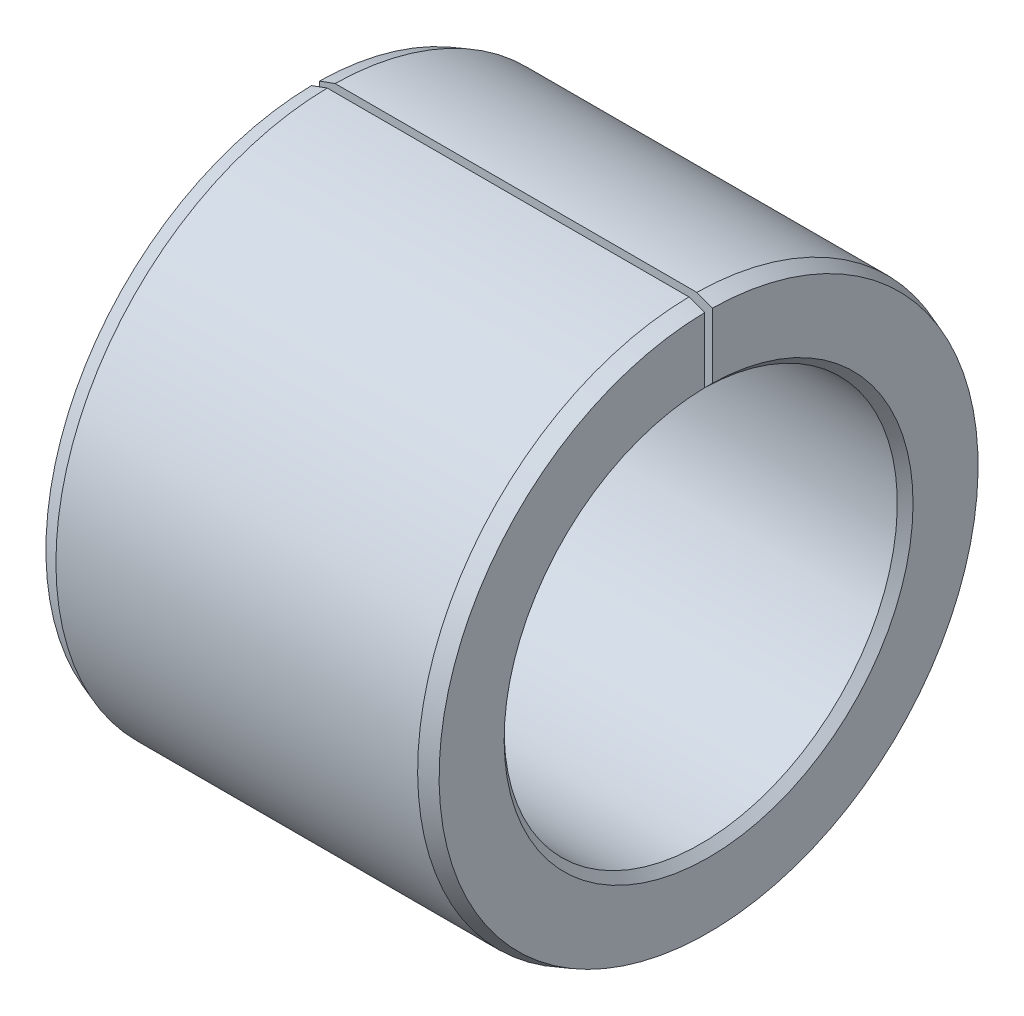
SolidWorks part; units mm, degrees
ref_plane "前视基准面" through (0, 0, 0) normal (0, 0, 1) x (1, 0, 0)
ref_plane "上视基准面" through (0, 0, 0) normal (0, 1, 0) x (1, 0, 0)
ref_plane "右视基准面" through (0, 0, 0) normal (1, 0, 0) x (0, 0, -1)
sketch "草图1" plane through (0, 0, 0) normal (0, 0, 1) x (1, 0, 0)
  line L0 (0, 0) -> (0, 3.4272) construction
  line L1 (0, 0) -> (4.8498, 0) construction
  line L2 (0.2, 3.5) -> (4.8, 3.5)
  line L3 (5, 3.4272) -> (5, 2.6)
  line L4 (4.9, 2.5) -> (0.1, 2.5)
  line L5 (0, 2.6) -> (0, 3.4272)
  line L6 (4.8, 3.5) -> (5, 3.4272)
  line L7 (5, 2.6) -> (4.9, 2.5)
  line L8 (0.1, 2.5) -> (0, 2.6)
  line L9 (0, 3.4272) -> (0.2, 3.5)
  point P6 (5, 2.5)
  point P7 (0, 2.5)
  dimension "D1" = 20
  dimension "Di" = 5
  dimension "D0" = 7
  dimension "B" = 5
  dimension "D2" = 20
  dimension "C0" = 0.2
  dimension "Ci" = 0.1
  dimension "D3" = 45
  dimension "D4" = 45
revolve "旋转1" add sketch "草图1" angle 360 about L1
sketch "草图2" plane through (0, 0, 0) normal (1, 0, 0) x (0, 0, -1)
  line L0 (0, 0) -> (0, 3.5) construction
  line L1 (-0.05, 0) -> (0.05, 0)
  line L2 (0.05, 0) -> (0.05, 3.5)
  line L3 (-0.05, 0) -> (-0.05, 3.5)
  line L4 (-0.05, 3.5) -> (0.05, 3.5)
  dimension "D1" = 0.1
extrude "切除-拉伸1" cut sketch "草图2" along normal through all
